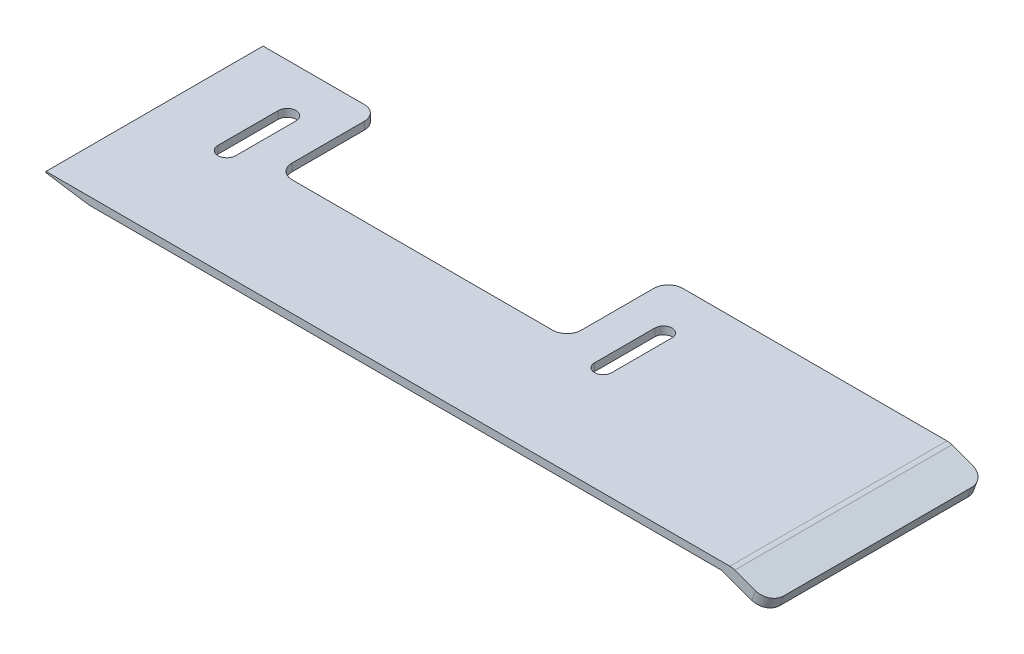
SolidWorks part; units mm, degrees
ref_plane "Front Plane" through (0, 0, 0) normal (0, 0, 1) x (1, 0, 0)
ref_plane "Top Plane" through (0, 0, 0) normal (0, 1, 0) x (1, 0, 0)
ref_plane "Right Plane" through (0, 0, 0) normal (1, 0, 0) x (0, 0, -1)
sketch "Sketch2" plane through (0, 0, 0) normal (0, 0, 1) x (1, 0, 0)
  line L0 (-70.922, 6.2188) -> (23.9466, 6.2188)
  line L1 (23.9466, 6.2188) -> (29.0209, 4.3719)
  line L2 (29.0209, 4.3719) -> (28.5079, 2.9624)
  line L3 (28.5079, 2.9624) -> (22.4676, 5.1608)
  line L4 (22.4676, 5.1608) -> (-64.922, 5.1608)
  line L5 (-64.922, 5.1608) -> (-70.922, 6.061)
  line L6 (-70.922, 6.061) -> (-70.922, 6.2188)
  dimension "D1" = 6
  dimension "D2" = 99.96
  dimension "D3" = 5.4
  dimension "D4" = 20
  dimension "D5" = 1.5
extrude "Boss-Extrude1" add sketch "Sketch2" along normal blind 30
fillet "Fillet10" radius 2 2 edges at (28.7644, 3.6671, 30) (28.7644, 3.6671, 0)
fillet "Fillet11" radius 2 1 edges at (23.9466, 6.2188, 15)
sketch "Sketch4" plane through (0, 5.1608, 0) normal (0, -1, 0) x (1, 0, 0)
  line L0 (-70.922, 30) -> (-70.922, 0) construction
  line L1 (-14.922, -2.4225) -> (-54.922, -2.4225)
  line L2 (-14.922, -2.4225) -> (-14.922, 14)
  line L3 (-14.922, 14) -> (-54.922, 14)
  line L4 (-54.922, -2.4225) -> (-54.922, 14)
  line L6 (-59.6886, 6.6742) -> (-59.6886, 15)
  line L8 (-62.1555, 6.6742) -> (-62.1555, 15)
  line L10 (-7.74, 6.6742) -> (-7.74, 15)
  line L12 (-10.1041, 6.6742) -> (-10.1041, 15)
  line L13 (-64.922, 0) -> (22.4676, 0) construction
  arc A0 (-59.6886, 15) -> (-62.1555, 15) centre (-60.922, 15) ccw
  arc A1 (-62.1555, 6.6742) -> (-59.6886, 6.6742) centre (-60.922, 6.6742) ccw
  arc A2 (-7.74, 15) -> (-10.1041, 15) centre (-8.922, 15) ccw
  arc A3 (-10.1041, 6.6742) -> (-7.74, 6.6742) centre (-8.922, 6.6742) ccw
  dimension "D1" = 16
  dimension "D2" = 56
  dimension "D5" = 14
extrude "Cut-Extrude1" cut sketch "Sketch4" against normal blind 30
fillet "Fillet12" radius 2 4 edges at (-54.922, 5.6898, 0) (-14.922, 5.6898, 0) (-14.922, 5.6898, 14) (-54.922, 5.6898, 14)
